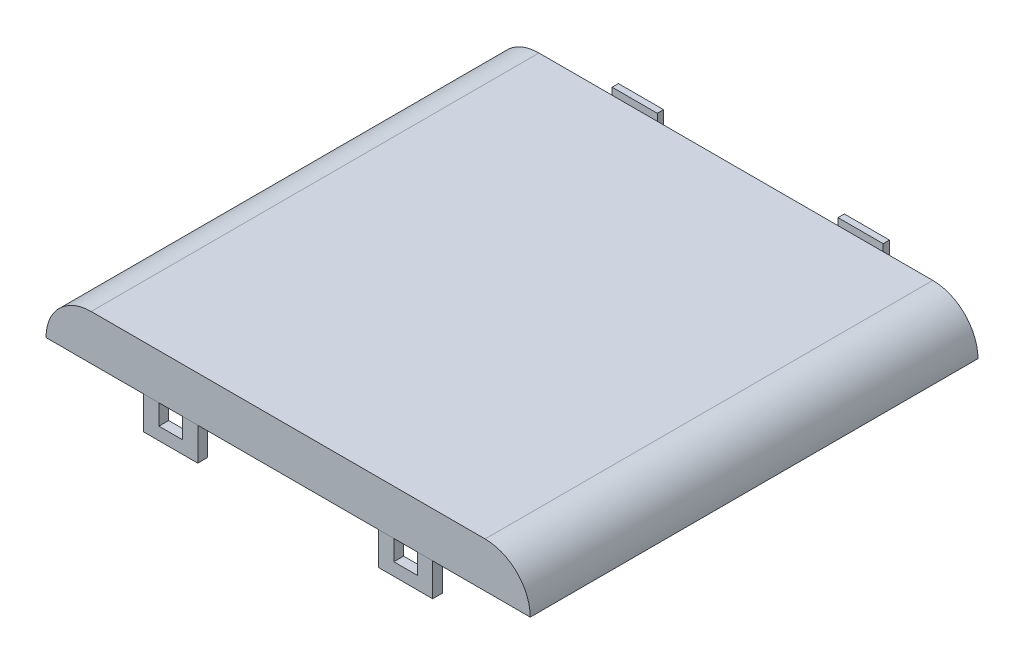
SolidWorks part; units mm, degrees
ref_plane "Front Plane" through (0, 0, 0) normal (0, 0, 1) x (1, 0, 0)
ref_plane "Top Plane" through (0, 0, 0) normal (0, 1, 0) x (1, 0, 0)
ref_plane "Right Plane" through (0, 0, 0) normal (1, 0, 0) x (0, 0, -1)
sketch "Sketch1" plane through (0, 0, 0) normal (0, 1, 0) x (1, 0, 0)
  line L1 (34.036, -31.4706) -> (-34.036, -31.4706)
  line L2 (34.036, -31.4706) -> (34.036, 31.4706)
  line L3 (34.036, 31.4706) -> (-34.036, 31.4706)
  line L4 (-34.036, -31.4706) -> (-34.036, 31.4706)
  line L5 (34.036, -31.4706) -> (-34.036, 31.4706) construction
  line L6 (34.036, 31.4706) -> (-34.036, -31.4706) construction
  point P0 (0, 0)
  dimension "D1" = 68.072
  dimension "D2" = 62.9412
extrude "Boss-Extrude1" add sketch "Sketch1" along normal blind 18.9103
fillet "Fillet1" radius 6.35 4 edges at (-34.036, 0, 0) (34.036, 0, 0) (34.036, 18.9103, 0) (-34.036, 18.9103, 0)
sketch "Sketch36" plane through (34.036, 0, 0) normal (1, 0, 0) x (0, 0, -1)
  line L0 (31.4706, 0) -> (-31.4706, 0) construction
  line L1 (-31.4706, 12.5603) -> (31.4706, 12.5603)
  line L2 (-31.4706, 12.5603) -> (-31.4706, 0)
  line L3 (-31.4706, 0) -> (31.4706, 0)
  line L4 (31.4706, 12.5603) -> (31.4706, 0)
  line L5 (31.4706, 12.5603) -> (31.4706, 18.9103) construction
extrude "Cut-Extrude13" cut sketch "Sketch36" against normal through all both and the other way through all
sketch "Sketch37" plane through (0, 0, 31.4706) normal (0, 0, 1) x (1, 0, 0)
  line L0 (-34.036, 12.5603) -> (34.036, 12.5603) construction
  line L1 (-20.32, 12.5603) -> (-12.7, 12.5603)
  line L2 (-20.32, 12.5603) -> (-20.32, 7.9375)
  line L3 (-20.32, 7.9375) -> (-12.7, 7.9375)
  line L4 (-12.7, 12.5603) -> (-12.7, 7.9375)
  line L5 (0, 0) -> (0, 12.5603) construction
  line L6 (14.859, 12.5603) -> (14.859, 9.7155)
  line L7 (-18.161, 12.5603) -> (-14.859, 12.5603)
  line L8 (-18.161, 12.5603) -> (-18.161, 9.7155)
  line L9 (-18.161, 9.7155) -> (-14.859, 9.7155)
  line L10 (-14.859, 12.5603) -> (-14.859, 9.7155)
  line L11 (18.161, 9.7155) -> (14.859, 9.7155)
  line L12 (18.161, 12.5603) -> (18.161, 9.7155)
  line L13 (18.161, 12.5603) -> (14.859, 12.5603)
  line L14 (12.7, 12.5603) -> (12.7, 7.9375)
  line L15 (20.32, 7.9375) -> (12.7, 7.9375)
  line L16 (20.32, 12.5603) -> (20.32, 7.9375)
  line L17 (20.32, 12.5603) -> (12.7, 12.5603)
  line M10 (-34.036, 12.5603) -> (34.036, 12.5603)
  dimension "D1" = 12.7
  dimension "D2" = 7.62
  dimension "D3" = 4.6228
  dimension "D4" = 1.778
  dimension "D5" = 2.159
  dimension "D6" = 2.159
extrude "Boss-Extrude2" add sketch "Sketch37" against normal blind 1.3716 separate body contours L10 L9 L8 L2 L3 L4 M10 | L16 L12 L11 L6 L14 L15 M10
shell "Shell1" thickness 1.3716
sketch "Sketch40" plane through (0, 0, -31.4706) normal (0, 0, -1) x (-1, 0, 0)
  line L0 (27.686, 15.8623) -> (-27.686, 15.8623)
  line L2 (-34.036, 12.5603) -> (34.036, 12.5603)
  line L3 (27.686, 18.9103) -> (-27.686, 18.9103)
  line L4 (-30.988, 12.5603) -> (30.988, 12.5603)
  line L6 (-28.956, 15.6083) -> (28.956, 15.6083) construction
  line L8 (-34.036, 12.5603) -> (34.036, 12.5603) construction
  line L9 (27.686, 18.9103) -> (-27.686, 18.9103) construction
  arc A2 (-27.686, 18.9103) -> (-34.036, 12.5603) centre (-27.686, 12.5603) ccw
  arc A3 (34.036, 12.5603) -> (27.686, 18.9103) centre (27.686, 12.5603) ccw
  arc A6 (30.988, 12.5603) -> (27.686, 15.8623) centre (27.686, 12.5603) ccw
  arc A7 (28.956, 15.6083) -> (27.686, 15.8623) centre (27.686, 12.5603) ccw construction
  arc A8 (-27.686, 15.8623) -> (-28.956, 15.6083) centre (-27.686, 12.5603) ccw construction
  arc A9 (-27.686, 15.8623) -> (-30.988, 12.5603) centre (-27.686, 12.5603) ccw
  arc A10 (-27.686, 18.9103) -> (-34.036, 12.5603) centre (-27.686, 12.5603) ccw construction
  arc A11 (34.036, 12.5603) -> (27.686, 18.9103) centre (27.686, 12.5603) ccw construction
  dimension "D1" = 0
  dimension "D2" = 3.048
extrude "Cut-Extrude14" cut sketch "Sketch40" against normal blind 1.3716
sketch "Sketch41" plane through (0, 0, -31.4706) normal (0, 0, -1) x (-1, 0, 0)
  line L0 (27.686, 15.8623) -> (-27.686, 15.8623) construction
  line L1 (-19.05, 15.8623) -> (-12.7, 15.8623)
  line L2 (-19.05, 15.8623) -> (-19.05, 19.5072)
  line L3 (-19.05, 19.5072) -> (-12.7, 19.5072)
  line L4 (-12.7, 15.8623) -> (-12.7, 19.5072)
  line L5 (-19.05, 18.2372) -> (-19.05, 17.2212) construction
  line L6 (12.7, 18.2372) -> (12.7, 17.2212) construction
  line L7 (12.7, 15.8623) -> (19.05, 15.8623)
  line L8 (12.7, 15.8623) -> (12.7, 19.5072)
  line L9 (12.7, 19.5072) -> (19.05, 19.5072)
  line L10 (19.05, 15.8623) -> (19.05, 19.5072)
extrude "Boss-Extrude4" add sketch "Sketch41" along normal blind 2.54
sketch "Sketch42" plane through (0, 0, -34.0106) normal (0, 0, -1) x (-1, 0, 0)
  line L0 (19.05, 15.8623) -> (19.05, 19.5072) construction
  line L1 (-19.05, 19.5072) -> (19.05, 19.5072)
  line L2 (-19.05, 19.5072) -> (-19.05, 18.2372)
  line L3 (-19.05, 18.2372) -> (19.05, 18.2372)
  line L4 (19.05, 19.5072) -> (19.05, 18.2372)
  dimension "D1" = 1.27
extrude "Cut-Extrude15" cut sketch "Sketch42" against normal up to surface (2.54 mm away) up to face at (-26.7492, 16.1108, -31.4706)
sketch "Sketch43" plane through (-19.05, 0, 0) normal (-1, 0, 0) x (0, 0, 1)
  line L0 (-31.4706, 18.2372) -> (-34.0106, 18.2372) construction
  line L1 (-33.1248, 18.2372) -> (-31.4706, 18.2372)
  line L2 (-33.1248, 18.2372) -> (-33.1248, 16.8258)
  line L3 (-33.1248, 16.8258) -> (-31.4706, 16.8258)
  line L4 (-31.4706, 18.2372) -> (-31.4706, 16.8258)
  line L5 (-31.4706, 15.8623) -> (-31.4706, 18.2372) construction
extrude "Cut-Extrude16" cut sketch "Sketch43" against normal through all
